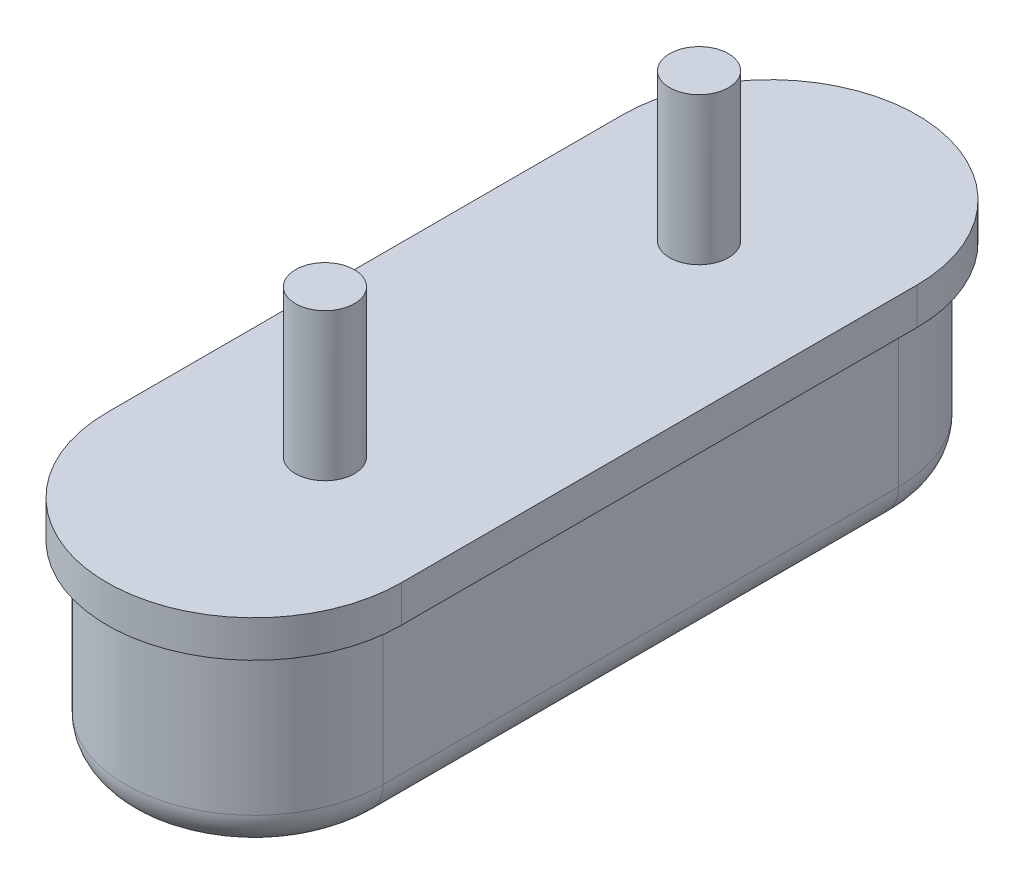
SolidWorks part; units mm, degrees
material "AISI 316 Stainless Steel Sheet (SS)"
ref_plane "Front Plane" through (0, 0, 0) normal (0, 0, 1) x (1, 0, 0)
ref_plane "Top Plane" through (0, 0, 0) normal (0, 1, 0) x (1, 0, 0)
ref_plane "Right Plane" through (0, 0, 0) normal (1, 0, 0) x (0, 0, -1)
ref_plane "Plane1" through (0, 0, 0) normal (0, -1, 0) x (1, 0, 0)
sketch "Sketch1" plane through (0, 0, 0) normal (0, -1, 0) x (1, 0, 0)
  line L0 (2, 3.5) -> (2, -3.5)
  line L1 (-2, 3.5) -> (-2, -3.5)
  arc A0 (2, 3.5) -> (-2, 3.5) centre (0, 3.5) ccw
  arc A1 (-2, -3.5) -> (2, -3.5) centre (0, -3.5) ccw
extrude "Boss-Extrude1" add sketch "Sketch1" along normal blind 3
sketch "Sketch2" plane through (0, -3, 0) normal (0, -1, 0) x (1, 0, 0)
  line L0 (1.75, 3.5) -> (1.75, -3.5)
  line L1 (-1.75, -3.5) -> (-1.75, 3.5)
  line L2 (2, 3.5) -> (2, -3.5)
  line L3 (-2, -3.5) -> (-2, 3.5)
  arc A0 (-1.75, -3.5) -> (1.75, -3.5) centre (0, -3.5) ccw
  arc A1 (1.75, 3.5) -> (-1.75, 3.5) centre (0, 3.5) ccw
  arc A2 (-2, -3.5) -> (2, -3.5) centre (0, -3.5) ccw
  arc A3 (2, 3.5) -> (-2, 3.5) centre (0, 3.5) ccw
extrude "Cut-Extrude1" cut sketch "Sketch2" against normal blind 2.5
fillet "Fillet1" radius 0.5 4 edges at (0, -3, -5.25) (1.75, -3, 0) (0, -3, 5.25) (-1.75, -3, 0)
sketch "Sketch3" plane through (0, 0, 0) normal (0, 1, 0) x (1, 0, 0)
  circle A0 centre (0, 2.54) radius 0.4
  circle A1 centre (0, -2.54) radius 0.4
  dimension "D3" = 0.8
  dimension "D1" = 2.54
  dimension "D2" = 2.54
extrude "Boss-Extrude2" add sketch "Sketch3" along normal blind 2
sketch "Sketch4" plane through (0, -3, 0) normal (0, -1, 0) x (1, 0, 0)
  line L0 (0.5, -3.3584) -> (0.5, 3.9041) construction
  line L1 (0, -2.75) -> (0, 2.75) construction
  text T0 "SPK16.000G" font "SWIsop3" height 1
  dimension "D1" = 0.5
extrude "Cut-Extrude2" cut sketch "Sketch4" against normal blind 0.05
fillet "Fillet2" radius 0.1 4 edges at (0, -0.5, -5.25) (-1.75, -0.5, 0) (0, -0.5, 5.25) (1.75, -0.5, 0)
